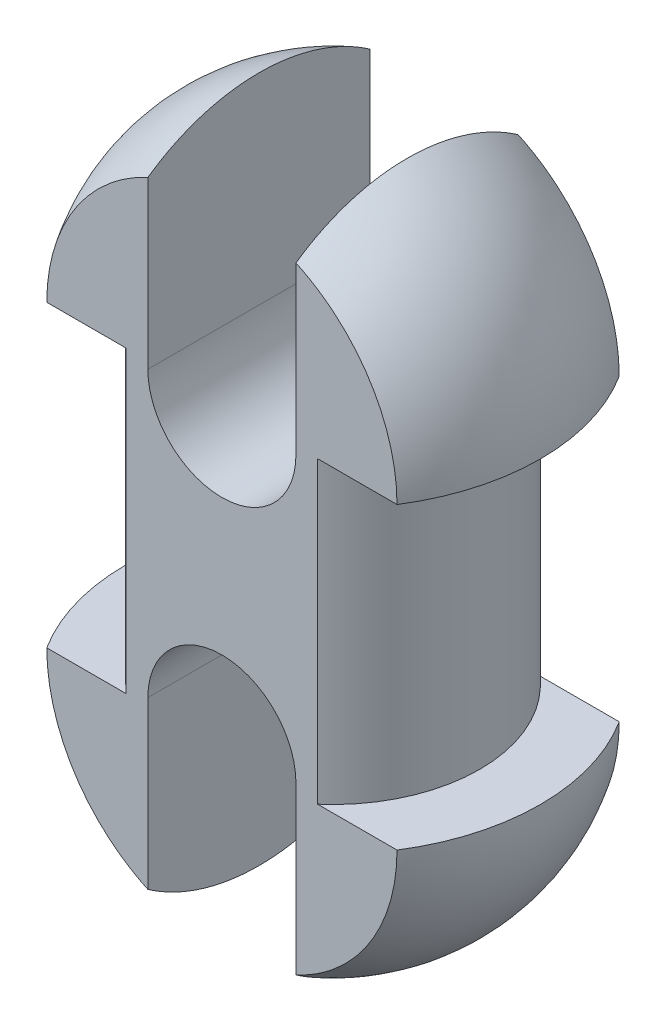
SolidWorks part; units mm, degrees
ref_plane "Plano frontal" through (0, 0, 0) normal (0, 0, 1) x (1, 0, 0)
ref_plane "Plano superior" through (0, 0, 0) normal (0, 1, 0) x (1, 0, 0)
ref_plane "Plano direito" through (0, 0, 0) normal (1, 0, 0) x (0, 0, -1)
sketch "Esboço1" plane through (0, 0, 0) normal (0, 0, 1) x (1, 0, 0)
  line L0 (0, -10.1) -> (0, 10.1) construction
  line L1 (-14, -10.1) -> (-14, 10.1)
  line L2 (14, -10.1) -> (14, 10.1)
  line L3 (14, 10.1) -> (9.9, 10.1)
  line L4 (9.9, 10.1) -> (9.9, -10.1)
  line L5 (9.9, -10.1) -> (14, -10.1)
  line L6 (0, 24.1) -> (0, -24.1)
  line L7 (0, -24.1) -> (0, 85.7647) construction
  arc A0 (-14, -10.1) -> (14, -10.1) centre (0, -10.1) ccw
  arc A1 (14, 10.1) -> (-14, 10.1) centre (0, 10.1) ccw
  point P2 (0, 0)
  dimension "D1" = 14
  dimension "D2" = 19.8
  dimension "D3" = 20.2
revolve "Revolução1" add sketch "Esboço1" angle 360 about L7
sketch "Esboço2" plane through (0, 0, 0) normal (0, 1, 0) x (1, 0, 0)
  line L1 (-14, -7.5) -> (14, -7.5)
  line L2 (-14, -7.5) -> (-14, 7.5)
  line L3 (-14, 7.5) -> (14, 7.5)
  line L4 (14, -7.5) -> (14, 7.5)
  line L5 (-14, -7.5) -> (14, 7.5) construction
  line L6 (-14, 7.5) -> (14, -7.5) construction
  circle A0 centre (0, 0) radius 14 construction
  point P0 (0, 0)
  dimension "D1" = 15
extrude "Corte-extrusão1" cut sketch "Esboço2" against normal through all both and the other way through all flip side to cut
sketch "Esboço3" plane through (0, 0, -7.5) normal (0, 0, -1) x (-1, 0, 0)
  line L0 (0, 24.1) -> (0, 9.6) construction
  line L1 (5, 24.1) -> (5, 9.6)
  line L2 (-5, 24.1) -> (-5, 9.6)
  line L3 (0, -24.1) -> (0, -9.6) construction
  line L4 (-5, -24.1) -> (-5, -9.6)
  line L5 (5, -24.1) -> (5, -9.6)
  arc A0 (14, 10.1) -> (-14, 10.1) centre (0, 10.1) ccw construction
  arc A1 (5, 24.1) -> (-5, 24.1) centre (0, 24.1) ccw
  arc A2 (-5, 9.6) -> (5, 9.6) centre (0, 9.6) ccw
  arc A3 (-14, -10.1) -> (14, -10.1) centre (0, -10.1) ccw construction
  arc A4 (-5, -24.1) -> (5, -24.1) centre (0, -24.1) ccw
  arc A5 (5, -9.6) -> (-5, -9.6) centre (0, -9.6) ccw
  point P6 (0, 16.85)
  point P11 (0, -16.85)
  dimension "D3" = 5
  dimension "D4" = 5
  dimension "D1" = 14.5
  dimension "D2" = 14.5
extrude "Corte-extrusão2" cut sketch "Esboço3" against normal through all
